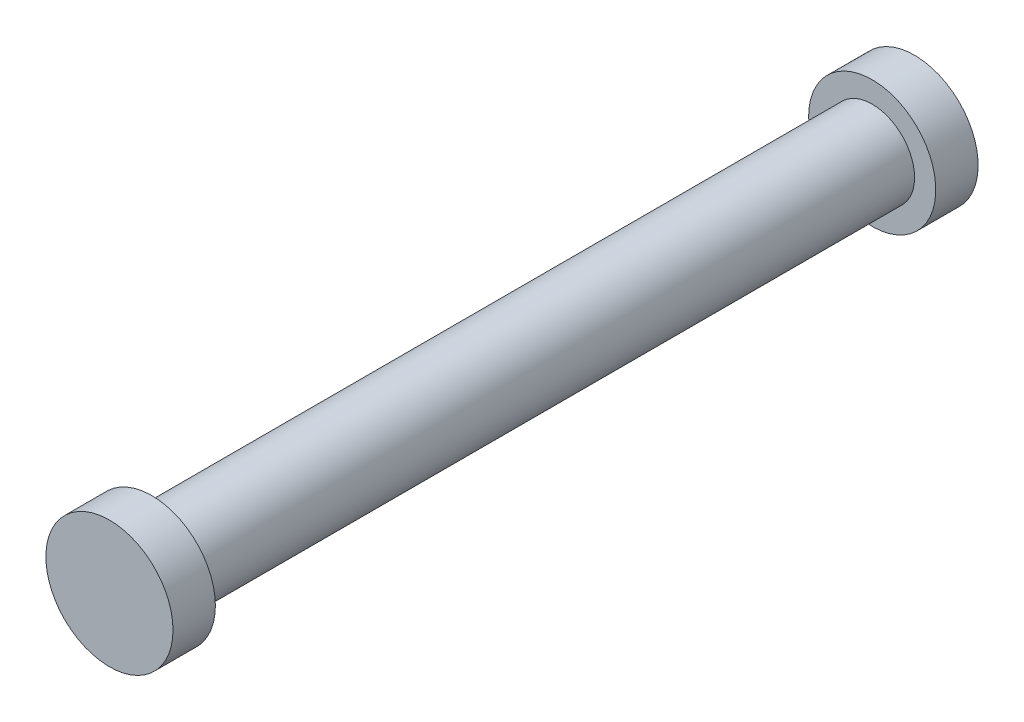
SolidWorks part; units mm, degrees
ref_plane "Front Plane" through (0, 0, 0) normal (0, 0, 1) x (1, 0, 0)
ref_plane "Top Plane" through (0, 0, 0) normal (0, 1, 0) x (1, 0, 0)
ref_plane "Right Plane" through (0, 0, 0) normal (1, 0, 0) x (0, 0, -1)
sketch "Sketch2" plane through (0, 0, 0) normal (0, 0, 1) x (1, 0, 0)
  circle A0 centre (0, 0) radius 2
extrude "Boss-Extrude1" add sketch "Sketch2" along normal blind 34
sketch "Sketch3" plane through (0, 0, 34) normal (0, 0, 1) x (1, 0, 0)
  circle A0 centre (0, 0) radius 3
extrude "Boss-Extrude2" add sketch "Sketch3" along normal blind 2
sketch "Sketch4" plane through (0, 0, 0) normal (0, 0, -1) x (-1, 0, 0)
  circle A0 centre (0, 0) radius 3
extrude "Boss-Extrude3" add sketch "Sketch4" along normal blind 2
